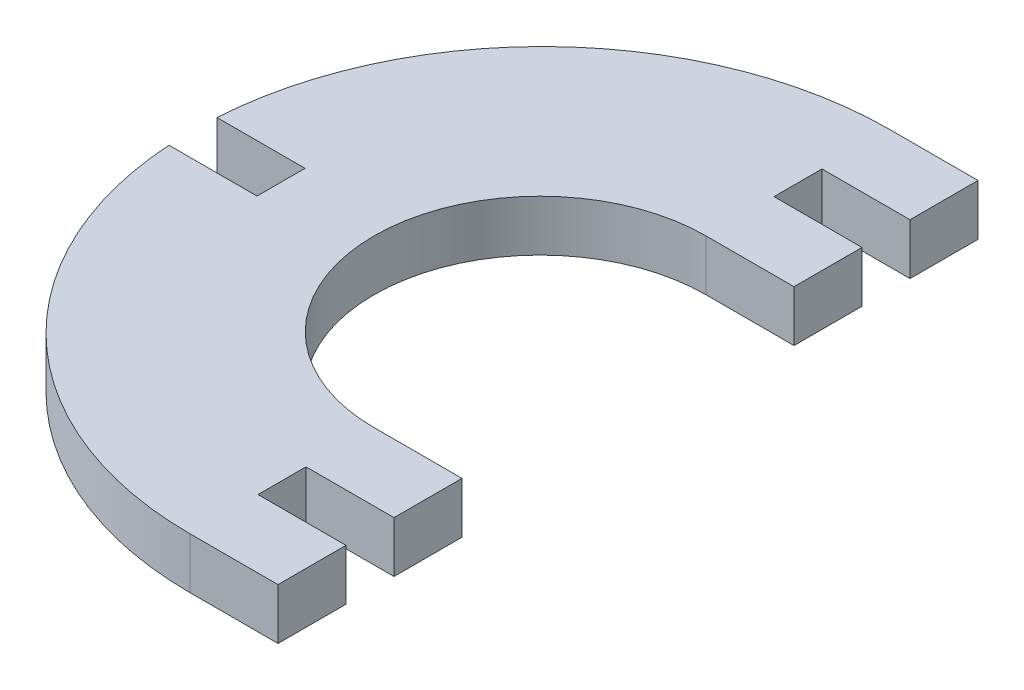
SolidWorks part; units mm, degrees
material "Balsa"
ref_plane "Alzado" through (0, 0, 0) normal (0, 0, 1) x (1, 0, 0)
ref_plane "Planta" through (0, 0, 0) normal (0, 1, 0) x (1, 0, 0)
ref_plane "Vista lateral" through (0, 0, 0) normal (1, 0, 0) x (0, 0, -1)
sketch "Croquis1" plane through (0, 0, 0) normal (0, 1, 0) x (1, 0, 0)
  line L0 (0, 0) -> (0, 6.8)
  line L1 (0, 6.8) -> (-8.8, 6.8)
  line L2 (-8.8, 6.8) -> (-8.8, 11.6)
  line L3 (-8.8, 11.6) -> (0, 11.6)
  line L4 (0, 11.6) -> (0, 18.4)
  line L5 (0, 18.4) -> (-8.8, 18.4)
  line L6 (0, 0) -> (-8.8, 0)
  line L7 (-8.8, 51.6) -> (0, 51.6)
  line L8 (0, 51.6) -> (0, 58.4)
  line L9 (0, 58.4) -> (-8.8, 58.4)
  line L10 (-8.8, 58.4) -> (-8.8, 63.2)
  line L11 (-8.8, 63.2) -> (0, 63.2)
  line L12 (0, 63.2) -> (0, 70)
  line L13 (0, 70) -> (-8.8, 70)
  line L14 (-25.4, 35) -> (-25.723, 35) construction
  line L15 (-34.7, 37.4) -> (-34.7, 32.6)
  line L16 (-34.7, 32.6) -> (-43.5, 32.6)
  line L17 (-34.7, 37.4) -> (-43.5, 37.4)
  arc A1 (-8.8, 51.6) -> (-8.8, 18.4) centre (-8.8, 35) ccw
  arc A2 (-8.8, 0) -> (-43.5, 32.6) centre (-8.8, 34.7676) cw
  arc A3 (-8.8, 70) -> (-43.5, 37.4) centre (-8.8, 35.2324) ccw
  point P26 (-34.7, 35)
extrude "Saliente-Extruir1" add sketch "Croquis1" along normal blind 5.1
equation "\"ranura\"=4.8"
equation "\"D2@Croquis1\"=\"ranura\""
equation "\"D4@Croquis1\"=\"ranura\"+4"
equation "\"Material\" =5.1"
equation "\"D1@Saliente-Extruir1\"=\"Material\""
equation "\"Altura\"= 70"
equation "\"D6@Croquis1\"=\"Altura\""
equation "\"D5@Croquis1\"=\"D4@Croquis1\"+0.5"
equation "\"D3@Croquis1\"=\"ranura\"+4"
equation "\"D1@Croquis1\"=\"D2@Croquis1\"+2"
